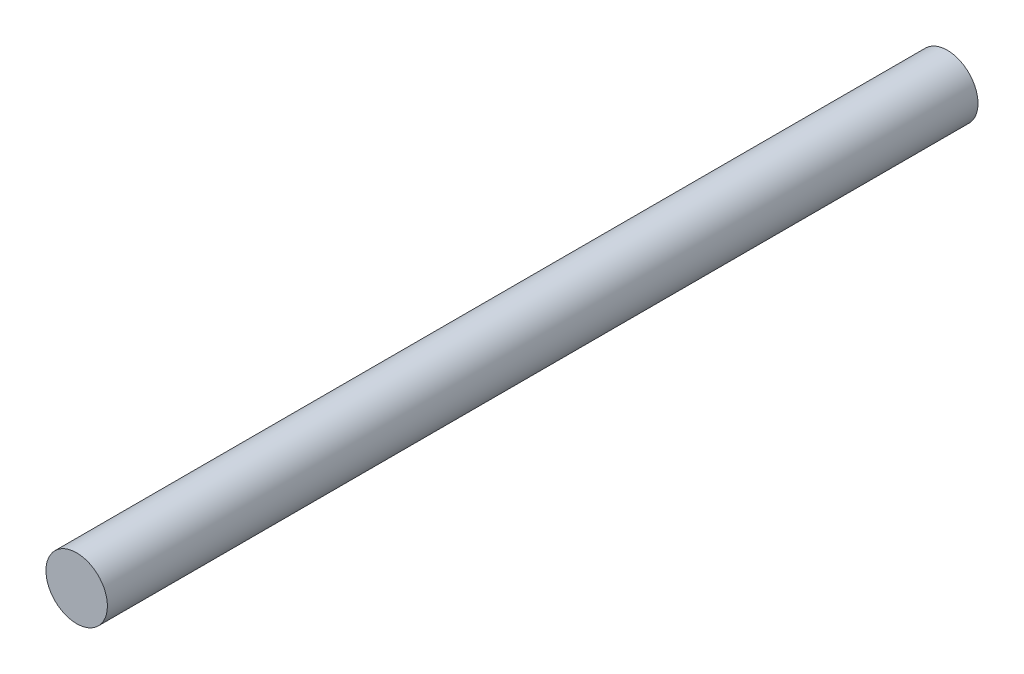
SolidWorks part; units mm, degrees
ref_plane "Front Plane" through (0, 0, 0) normal (0, 0, 1) x (1, 0, 0)
ref_plane "Top Plane" through (0, 0, 0) normal (0, 1, 0) x (1, 0, 0)
ref_plane "Right Plane" through (0, 0, 0) normal (1, 0, 0) x (0, 0, -1)
sketch "Sketch1" plane through (0, 0, 0) normal (0, 0, 1) x (1, 0, 0)
  circle A0 centre (0, 0) radius 6
  dimension "D1" = 12
extrude "Boss-Extrude1" add sketch "Sketch1" along normal mid plane 170
